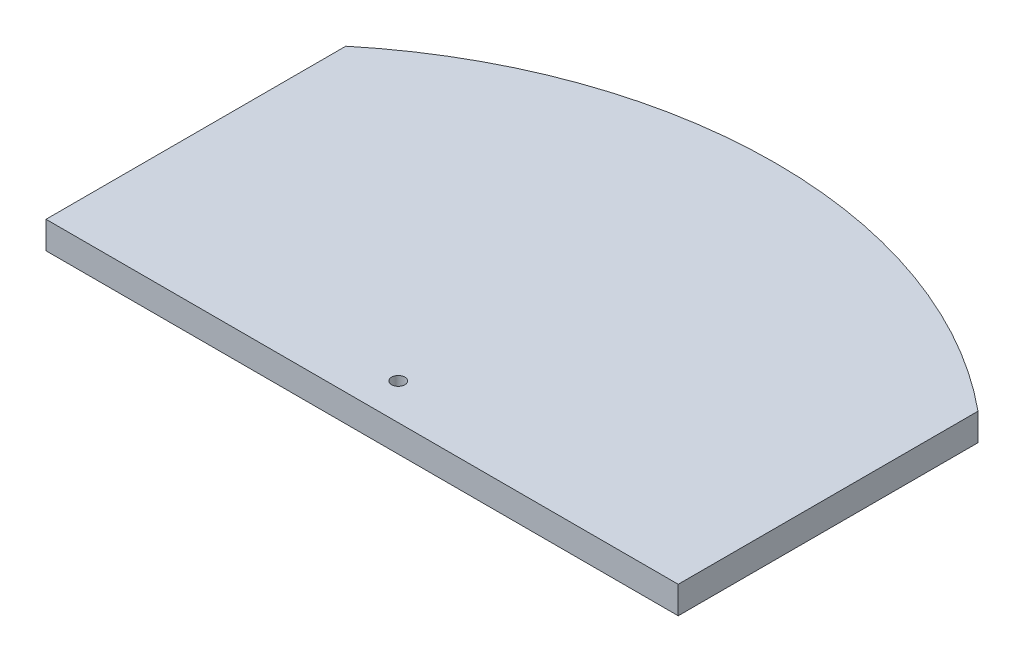
SolidWorks part; units mm, degrees
ref_plane "Front Plane" through (0, 0, 0) normal (0, 0, 1) x (1, 0, 0)
ref_plane "Top Plane" through (0, 0, 0) normal (0, 1, 0) x (1, 0, 0)
ref_plane "Right Plane" through (0, 0, 0) normal (1, 0, 0) x (0, 0, -1)
sketch "Sketch1" plane through (0, 0, 0) normal (0, 1, 0) x (1, 0, 0)
  line L0 (-47.45, -31.6854) -> (-47.45, -76.6854)
  line L1 (0, 0) -> (0, -76.6854) construction
  line L2 (47.45, -31.6854) -> (47.45, -76.6854)
  line L3 (-47.45, -76.6854) -> (47.45, -76.6854)
  arc A0 (-47.45, -31.6854) -> (47.45, -31.6854) centre (0, -89.1201) cw
  circle A1 centre (0, -71.2603) radius 1
  dimension "D3" = 74.5
  dimension "D4" = 2
  dimension "D1" = 94.9
  dimension "D2" = 45
extrude "Boss-Extrude1" add sketch "Sketch1" along normal blind 4.1
